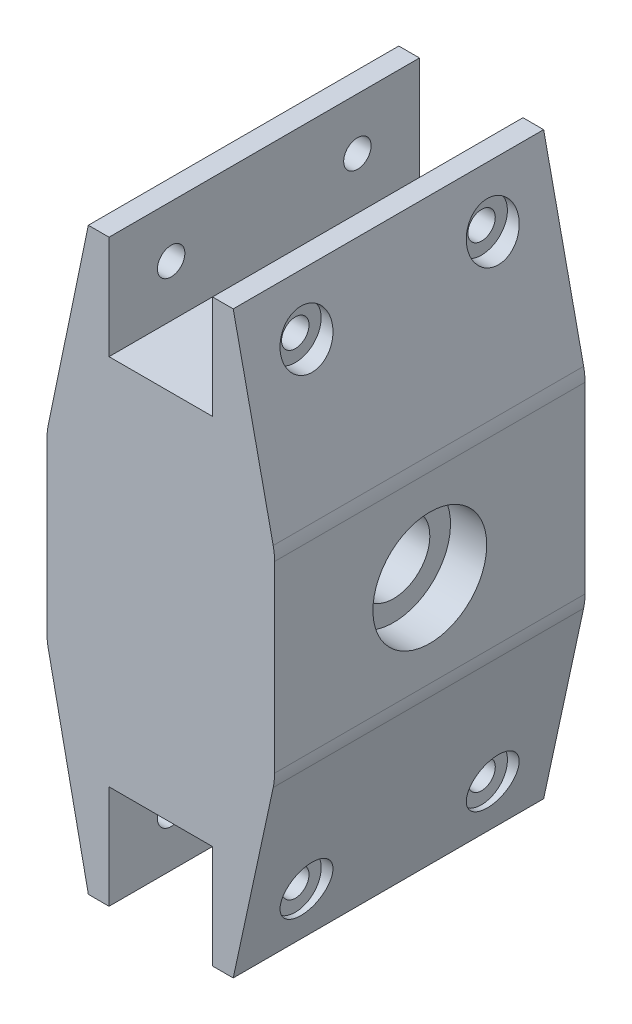
SolidWorks part; units mm, degrees
ref_plane "Front" through (0, 0, 0) normal (0, 0, 1) x (1, 0, 0)
ref_plane "Top" through (0, 0, 0) normal (0, 1, 0) x (1, 0, 0)
ref_plane "Right" through (0, 0, 0) normal (1, 0, 0) x (0, 0, -1)
sketch "Sketch1" plane through (0, 0, 0) normal (0, 0, 1) x (1, 0, 0)
  line L0 (-10, 36) -> (-10, 56)
  line L1 (-10, -36) -> (10, -36)
  line L2 (-10, -36) -> (-10, 36)
  line L3 (-10, 36) -> (10, 36)
  line L4 (10, -36) -> (10, 36)
  line L5 (-10, -36) -> (10, 36) construction
  line L6 (-10, 36) -> (10, -36) construction
  line L7 (-10, 56) -> (-14, 56)
  line L8 (-14, 56) -> (-22, 17.5)
  line L9 (-22, 17.5) -> (-22, -17.5)
  line L10 (-22, -17.5) -> (-14, -56)
  line L11 (-14, -56) -> (-10, -56)
  line L12 (-10, -56) -> (-10, -36)
  line L13 (0, 0) -> (0, 36) construction
  line L14 (10, -56) -> (10, -36)
  line L15 (14, -56) -> (10, -56)
  line L16 (22, -19) -> (14, -56)
  line L17 (22, 19) -> (22, -19)
  line L18 (14, 56) -> (22, 19)
  line L19 (10, 56) -> (14, 56)
  line L20 (10, 36) -> (10, 56)
  line L21 (14, 56) -> (14, -56)
  point P0 (0, 0)
  dimension "D1" = 72
  dimension "D2" = 20
  dimension "D3" = 4
  dimension "D4" = 20
  dimension "D5" = 20
  dimension "D6" = 4
  dimension "D7" = 12
  dimension "D8" = 35
  dimension "D9" = 17.5
  dimension "D10" = 12
  dimension "D11" = 38
  dimension "D12" = 19
extrude "Boss-Extrude1" add sketch "Sketch1" along normal blind 60 contours L20 L4 L14 L15 L16 L17 L18 L19 | L1 L4 L3 L2 | L11 L12 L2 L0 L7 L8 L9 L10 | L18 L21 L16 L17
sketch "Sketch2" plane through (-22, 0, 0) normal (-1, 0, 0) x (0, 0, 1)
  line L0 (0, 0) -> (60, 0) construction
  line L1 (60, 17.5) -> (60, -17.5) construction
  circle A0 centre (30, 0) radius 7
  dimension "D1" = 14
extrude "Cut-Extrude1" cut sketch "Sketch2" against normal through all
sketch "Sketch3" plane through (-22, 0, 0) normal (-1, 0, 0) x (0, 0, 1)
  circle A0 centre (30, 0) radius 11
  dimension "D1" = 22
extrude "Cut-Extrude2" cut sketch "Sketch3" against normal blind 7
sketch "Sketch4" plane through (22, 0, 0) normal (1, 0, 0) x (0, 0, -1)
  circle A0 centre (-30, 0) radius 11 construction
  circle A1 centre (-30, 0) radius 11
extrude "Cut-Extrude3" cut sketch "Sketch4" against normal blind 7
ref_plane "Plane1" through (-18, 0, 0) normal (1, 0, 0) x (0, 0, -1)
sketch "Sketch5" plane through (-18, 0, 0) normal (1, 0, 0) x (0, 0, -1)
  line L0 (-60, 56) -> (0, 56) construction
  line L1 (0, 56) -> (0, 17.5) construction
  line L2 (-60, 56) -> (-60, 17.5) construction
  line L3 (-30, 56) -> (-30, 46) construction
  circle A0 centre (-12, 46) radius 2.65
  circle A1 centre (-48, 46) radius 2.65
  dimension "D1" = 10
  dimension "D3" = 12
  dimension "D5" = 5.3
  dimension "D6" = 5.3
  dimension "D2" = 12
extrude "Cut-Extrude4" cut sketch "Sketch5" along normal through all
sketch "Sketch6" plane through (-18, 0, 0) normal (1, 0, 0) x (0, 0, -1)
  circle A0 centre (-12, 46) radius 5
  circle A2 centre (-48, 46) radius 5
  dimension "D1" = 10
  dimension "D3" = 10
extrude "Cut-Extrude5" cut sketch "Sketch6" along normal blind 4
mirror "Mirror3" about plane through (0, 0, 0) normal (0, 1, 0) of "Cut-Extrude5", "Cut-Extrude4"
fillet "Fillet1" radius 12 4 edges at (-22, -17.5, 30) (-22, 17.5, 30) (22, -19, 30) (22, 19, 30)
ref_plane "Plane2" through (18, 0, 0) normal (-1, 0, 0) x (0, 0, 1)
sketch "Sketch7" plane through (18, 0, 0) normal (-1, 0, 0) x (0, 0, 1)
  circle A0 centre (12, 46) radius 5 construction
  circle A1 centre (48, 46) radius 5 construction
  circle A2 centre (12, 46) radius 5
  circle A3 centre (48, 46) radius 5
extrude "Cut-Extrude6" cut sketch "Sketch7" along normal blind 4
mirror "Mirror5" about plane through (0, 0, 0) normal (0, 1, 0) of "Cut-Extrude6"
